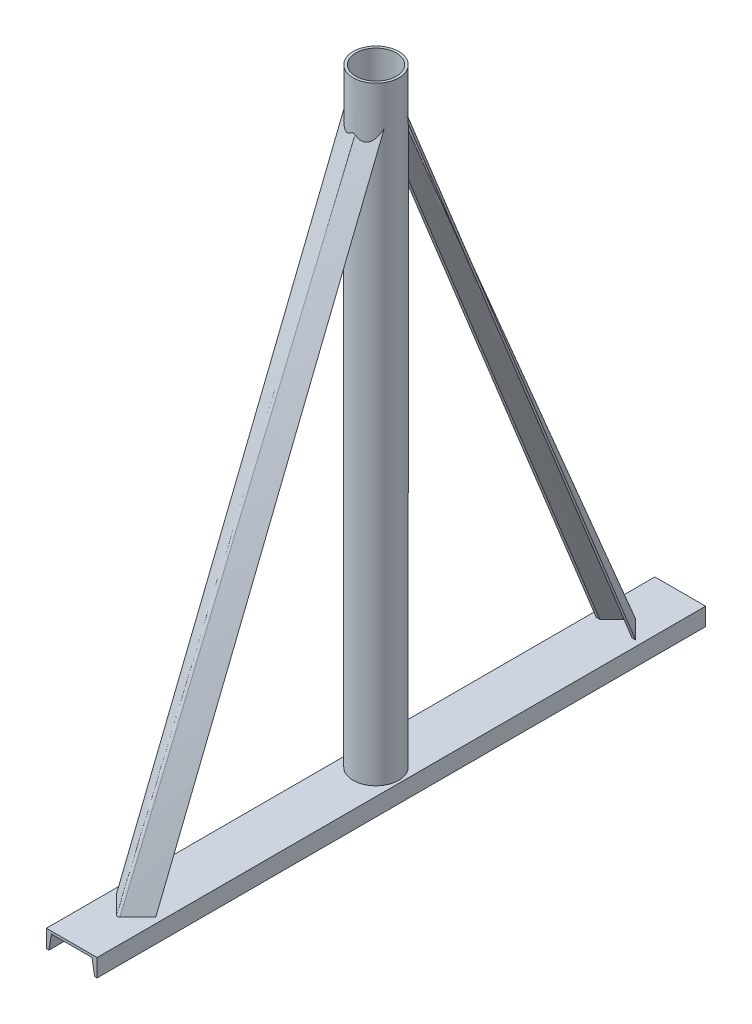
SolidWorks part; units mm, degrees
material "ASTM A36 Steel"
ref_plane "Front Plane" through (0, 0, 0) normal (0, 0, 1) x (1, 0, 0)
ref_plane "Top Plane" through (0, 0, 0) normal (0, 1, 0) x (1, 0, 0)
ref_plane "Right Plane" through (0, 0, 0) normal (1, 0, 0) x (0, 0, -1)
sketch "Sketch1" plane through (0, 0, 0) normal (0, 0, 1) x (1, 0, 0)
  line L0 (63.5, 0) -> (-63.5, 0)
  line L1 (-63.5, 0) -> (-63.5, -44.45)
  line L2 (-63.5, -44.45) -> (-57.15, -44.45)
  line L3 (-57.15, -44.45) -> (-50.8, -6.35)
  line L4 (-50.8, -6.35) -> (50.8, -6.35)
  line L5 (50.8, -6.35) -> (57.15, -44.45)
  line L6 (57.15, -44.45) -> (63.5, -44.45)
  line L7 (63.5, -44.45) -> (63.5, 0)
  point P4 (0, 0)
  dimension "D1" = 127
  dimension "D2" = 44.45
  dimension "D3" = 6.35
  dimension "D4" = 6.35
  dimension "D5" = 6.35
  dimension "D6" = 12.7
  dimension "D7" = 12.7
  dimension "D8" = 44.45
extrude "Boss-Extrude1" add sketch "Sketch1" along normal blind 1524
sketch "Sketch2" plane through (0, 0, 0) normal (0, 1, 0) x (1, 0, 0)
  line L0 (-63.5, -1524) -> (-63.5, 0) construction
  line L1 (63.5, 0) -> (-63.5, 0) construction
  circle A0 centre (0, -762) radius 57.15
  circle A1 centre (0, -762) radius 50.8
  dimension "D1" = 114.3
  dimension "D4" = 101.6
  dimension "D2" = 63.5
  dimension "D3" = 762
extrude "Boss-Extrude2" add sketch "Sketch2" along normal blind 1524
sketch "Sketch4" plane through (0, 0, 0) normal (0, 1, 0) x (1, 0, 0)
  line L0 (4.4901, -116.1599) -> (49.3914, -161.0612)
  line L1 (49.3914, -161.0612) -> (40.4112, -161.0612)
  line L2 (40.4112, -161.0612) -> (1.7961, -122.4461)
  line L3 (-1.7961, -122.4461) -> (-40.4112, -161.0612)
  line L5 (-49.3914, -161.0612) -> (-4.4901, -116.1599)
  line L6 (-63.5, -1524) -> (-63.5, 0) construction
  line L7 (-49.3914, -161.0612) -> (-40.4112, -161.0612)
  arc A0 (1.7961, -122.4461) -> (-1.7961, -122.4461) centre (0, -124.2421) ccw
  arc A1 (4.4901, -116.1599) -> (-4.4901, -116.1599) centre (0, -120.65) ccw
  point P11 (0, -114.3)
  dimension "D1" = 2.54
  dimension "D2" = 6.35
  dimension "D3" = 6.35
  dimension "D4" = 6.35
  dimension "D5" = 63.5
  dimension "D6" = 63.5
  dimension "D7" = 120.65
  dimension "D8" = 63.5
  dimension "D9" = 8.9803
sketch3d "3DSketch2"
  spline S0 degree 3 poles (-7.3718, 1473.1096, 705.2534) (-1.2839, 1478.9872, 704.7675) (4.1656, 1469.671, 704.8922) (9.5635, 1464.7388, 705.6023) (13.076, 1456.6487, 706.3424) (16.2324, 1448.9872, 707.1568) (21.2675, 1438.8323, 708.8223) (26.9081, 1427.1565, 711.5144) (30.3868, 1416.802, 713.4657) (38.5607, 1401.0005, 719.1807) (27.5419, 1404.2189, 711.7737) (27.0669, 1412.0536, 711.7228) (23.5545, 1419.4207, 709.7944) (18.6312, 1426.267, 707.9304) (15.6148, 1433.6889, 706.9945) (11.9739, 1439.9852, 706.0885) (9.8008, 1446.2756, 705.6586) (5.8188, 1452.1094, 705.1244) (4.0754, 1457.4579, 704.9076) (-3.1862, 1466.7538, 704.8387) (-4.7151, 1453.2421, 705.05) (-8.5173, 1445.8872, 705.4387) (-12.0778, 1435.4509, 706.0806) (-17.2132, 1427.1055, 707.4026) (-20.693, 1418.8923, 708.7794) (-20.4319, 1410.4872, 708.4052) (-33.2389, 1406.8746, 714.8549) (-24.0624, 1422.9106, 710.0638) (-21.896, 1432.791, 709.1987) (-17.9207, 1443.6541, 707.672) (-14.5671, 1455.2022, 706.7196) (-12.0555, 1466.2517, 706.0871) (-7.3718, 1473.1096, 705.2534) (-1.2839, 1478.9872, 704.7675) (4.1656, 1469.671, 704.8922) knots -0.089732 -0.042042 -0.018199 0 0.027232 0.062192 0.082492 0.114742 0.147362 0.199931 0.241801 0.284824 0.31024 0.328594 0.359562 0.394688 0.415876 0.441238 0.468918 0.483632 0.511323 0.534532 0.565549 0.597261 0.63301 0.672907 0.698298 0.724819 0.748944 0.797179 0.832754 0.871454 0.910268 0.957958 0.981801 1 1.027232 1.062192 1.082492 only from (-2.2242, 1476.7574, 704.8933) to (-2.2242, 1476.7574, 704.8933)
ref_plane "Plane1" through (0, 0, 762) normal (0, 0, 1) x (1, 0, 0)
sketch "Sketch5" plane through (0, 0, 762) normal (0, 0, 1) x (1, 0, 0)
  line L1 (-104.2094, 1606.4672) -> (87.6812, 1606.4672)
  line L2 (-104.2094, 1606.4672) -> (-104.2094, 4.8804)
  line L3 (-104.2094, 4.8804) -> (87.6812, 4.8804)
  line L4 (87.6812, 1606.4672) -> (87.6812, 4.8804)
extrude "Cut-Extrude1" cut sketch "Sketch5" along normal blind 826.77
ref_plane "Plane2" through (0, 0, 736.6) normal (0, 0, 1) x (1, 0, 0)
sketch "Sketch8" plane through (0, 0, 736.6) normal (0, 0, 1) x (1, 0, 0)
  line L0 (4.4901, 1477.6901) -> (49.3914, 1432.7888)
  line L1 (49.3914, 1432.7888) -> (40.4112, 1432.7888)
  line L2 (40.4112, 1432.7888) -> (1.7961, 1471.4039)
  line L3 (-1.7961, 1471.4039) -> (-40.4112, 1432.7888)
  line L4 (-49.3914, 1432.7888) -> (-4.4901, 1477.6901)
  line L5 (-49.3914, 1432.7888) -> (-40.4112, 1432.7888)
  line L6 (57.15, 1524) -> (-57.15, 1524) construction
  arc A0 (1.7961, 1471.4039) -> (-1.7961, 1471.4039) centre (0, 1469.6079) ccw
  arc A1 (4.4901, 1477.6901) -> (-4.4901, 1477.6901) centre (0, 1473.2) ccw
  point P11 (0, 0)
  point P14 (0, 1524)
  dimension "D1" = 2.54
  dimension "D2" = 6.35
  dimension "D3" = 6.35
  dimension "D4" = 6.35
  dimension "D5" = 63.5
  dimension "D6" = 63.5
  dimension "D7" = 8.9803
  dimension "D8" = 50.8
loft "Loft6" add profiles "Sketch8", "Sketch4"
ref_plane "Plane3" through (0, 1549.4, 0) normal (0, 1, 0) x (1, 0, 0)
mirror "Mirror1" about plane through (0, 0, 762) normal (0, 0, 1) of "Boss-Extrude2", "Loft6"
sketch "Sketch11" plane through (0, 1549.4, 0) normal (0, 1, 0) x (1, 0, 0)
  circle A0 centre (0, -762) radius 50.8
extrude "Cut-Extrude3" cut sketch "Sketch11" against normal blind 826.77
